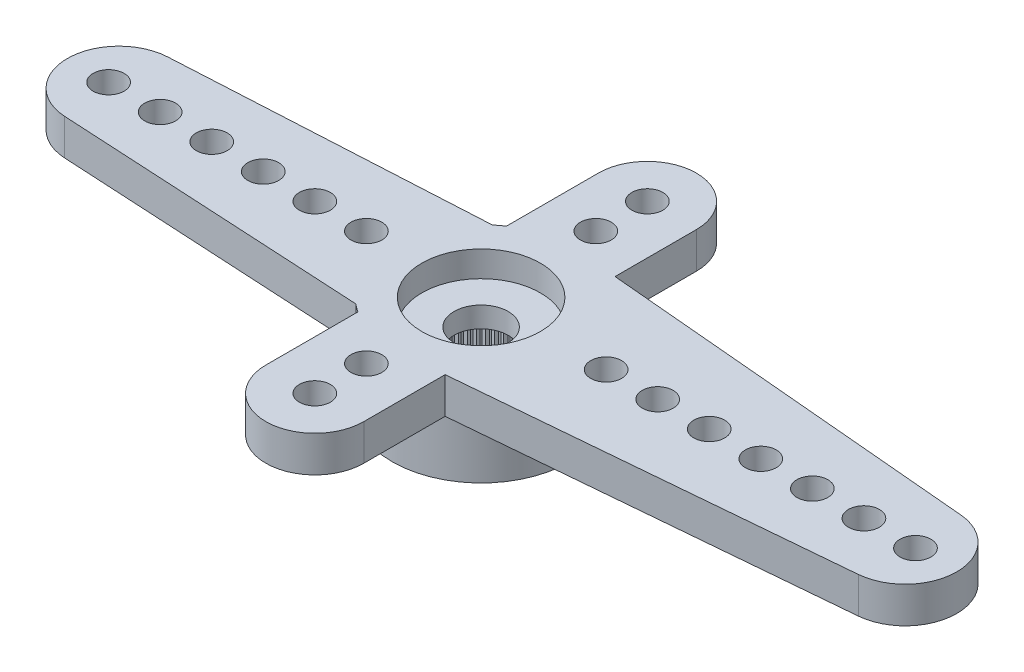
SolidWorks part; units mm, degrees
material "PVC Rígido"
ref_plane "Plano frontal" through (0, 0, 0) normal (0, 0, 1) x (1, 0, 0)
ref_plane "Plano superior" through (0, 0, 0) normal (0, 1, 0) x (1, 0, 0)
ref_plane "Plano direito" through (0, 0, 0) normal (1, 0, 0) x (0, 0, -1)
sketch "Esboço1" plane through (0, 0, 0) normal (0, 1, 0) x (1, 0, 0)
  line L0 (0, 0) -> (-14.05, 0) construction
  line L1 (-14.1591, 1.997) -> (-2.2091, 2.65)
  line L2 (-2.2091, -2.65) -> (-14.1591, -1.997)
  arc A0 (-2.2091, -2.65) -> (-2.2091, 2.65) centre (0, 0) ccw
  arc A1 (-14.1591, 1.997) -> (-14.1591, -1.997) centre (-14.05, 0) ccw
  dimension "D1" = 6.9
  dimension "D2" = 4
  dimension "D3" = 19.5
  dimension "D4" = 5.3
extrude "Ressalto-extrusão1" add sketch "Esboço1" against normal blind 1.4
sketch "Esboço2" plane through (0, -1.4, 0) normal (0, -1, 0) x (1, 0, 0)
  arc A0 (-2.2091, -2.65) -> (-2.2091, 2.65) centre (0, 0) ccw construction
  circle A1 centre (0, 0) radius 3.45
extrude "Ressalto-extrusão2" add sketch "Esboço2" along normal offset from surface (2.4 mm away) 3.8 up to face at (-7.242, 0, 0)
hole_wizard "Furo1" positions "Esboço9" profile "Esboço10" legacy end condition through all
sketch "Esboço9" plane through (0, 0, 0) normal (0, 1, 0) x (1, 0, 0)
  line L1 (-14.45, 0) -> (0, 0) construction
  arc A2 (-14.1591, 1.997) -> (-14.1591, -1.997) centre (-14.05, 0) ccw construction
  point P0 (-14.45, 0)
  point P19 (-16.05, 0)
  dimension "D1" = 1.6
sketch "Esboço10" plane through (-14.45, 0, 0) normal (1, 0, 0) x (0, 0, 1)
  line L0 (0, 0) -> (0, 3.8)
  line L1 (0, 3.8) -> (0.6, 3.8)
  line L2 (0.6, 3.8) -> (0.6, 0)
  line L3 (0.6, 0) -> (0, 0)
  line L4 (0, 110) -> (0, -10) construction
  dimension "Diameter" = 1.2
  dimension "Depth" = 3.8
pattern_linear "Padrão linear1" count 6 spacing 2 along (1, 0, 0) of "Furo1"
sketch "Esboço12" plane through (0, 0, 0) normal (0, 1, 0) x (1, 0, 0)
  line L0 (0.3041, 3.4366) -> (16.6263, 1.9922)
  line L1 (16.6263, -1.9922) -> (0.3041, -3.4366)
  arc A0 (-2.2091, -2.65) -> (-2.2091, 2.65) centre (0, 0) ccw construction
  arc A1 (0.3041, -3.4366) -> (0.3041, 3.4366) centre (0, 0) ccw
  arc A2 (16.6263, 1.9922) -> (16.6263, -1.9922) centre (16.45, 0) cw
  arc A3 (-14.1591, 1.997) -> (-14.1591, -1.997) centre (-14.05, 0) ccw construction
  point P11 (0, 0)
  dimension "D1" = 2
  dimension "D2" = 34.5
extrude "Ressalto-extrusão3" add sketch "Esboço12" against normal up to surface (1.4 mm away) up to face at (-12.45, -1.4, 0.6)
hole_wizard "Furo2" positions "Esboço13" profile "Esboço14" legacy end condition through all
sketch "Esboço13" plane through (0, 0, 0) normal (0, 1, 0) x (1, 0, 0)
  line L0 (0, 0) -> (16.85, 0) construction
  arc A0 (16.6263, -1.9922) -> (16.6263, 1.9922) centre (16.45, 0) ccw construction
  point P0 (16.85, 0)
  point P6 (18.45, 0)
  dimension "D1" = 1.6
sketch "Esboço14" plane through (16.85, 0, 0) normal (1, 0, 0) x (0, 0, 1)
  line L0 (0, 0) -> (0, 3.8)
  line L1 (0, 3.8) -> (0.6, 3.8)
  line L2 (0.6, 3.8) -> (0.6, 0)
  line L3 (0.6, 0) -> (0, 0)
  line L4 (0, 110) -> (0, -10) construction
  dimension "Diameter" = 1.2
  dimension "Depth" = 3.8
pattern_linear "Padrão linear2" count 7 spacing 2 along (-1, 0, 0) of "Furo2"
sketch "Esboço16" plane through (0, 0, 0) normal (0, 1, 0) x (1, 0, 0)
  line L0 (0, -6.45) -> (0, 6.45) construction
  line L1 (-1.9, -6.45) -> (-1.9, 6.45)
  line L2 (1.9, -6.45) -> (1.9, 6.45)
  arc A0 (-1.9, -6.45) -> (1.9, -6.45) centre (0, -6.45) ccw
  arc A1 (1.9, 6.45) -> (-1.9, 6.45) centre (0, 6.45) ccw
  point P2 (0, 0)
  dimension "D2" = 16.7
  dimension "D1" = 3.8
extrude "Ressalto-extrusão4" add sketch "Esboço16" against normal up to surface (1.4 mm away) up to face at (14.85, -1.4, 0.6)
hole_wizard "Furo3" positions "Esboço17" profile "Esboço18" legacy end condition through all
sketch "Esboço17" plane through (0, 0, 0) normal (0, 1, 0) x (1, 0, 0)
  point P0 (0, -6.45)
sketch "Esboço18" plane through (0, 0, 6.45) normal (1, 0, 0) x (0, 0, 1)
  line L0 (0, 0) -> (0, 3.8)
  line L1 (0, 3.8) -> (0.6, 3.8)
  line L2 (0.6, 3.8) -> (0.6, 0)
  line L3 (0.6, 0) -> (0, 0)
  line L4 (0, 110) -> (0, -10) construction
  dimension "Diameter" = 1.2
  dimension "Depth" = 3.8
pattern_linear "Padrão linear3" count 2 spacing 2 along (0, 0, -1) of "Furo3"
pattern_circular "PadrãoCircular1" count 2 over 360 about axis through (0, 0, 0) along (0, 1, 0) of "Padrão linear3", "Furo3"
hole_wizard "Furo4" positions "Esboço3" profile "Esboço4" legacy
sketch "Esboço3" plane through (0, -3.8, 0) normal (0, -1, 0) x (-1, 0, 0)
  point P0 (0, 0)
sketch "Esboço4" plane through (0, -3.8, 0) normal (1, 0, 0) x (0, 0, -1)
  line L0 (0, 0) -> (0, 2)
  line L1 (0, 2) -> (2.475, 2)
  line L2 (2.475, 2) -> (2.475, 0)
  line L3 (2.475, 0) -> (0, 0)
  line L4 (0, 110) -> (0, -10) construction
  dimension "Diameter" = 4.95
  dimension "Depth" = 2
hole_wizard "Furo5" positions "Esboço5" profile "Esboço6" legacy
sketch "Esboço5" plane through (0, 0, 0) normal (0, 1, 0) x (1, 0, 0)
  point P0 (0, 0)
sketch "Esboço6" plane through (0, 0, 0) normal (1, 0, 0) x (0, 0, 1)
  line L0 (0, 0) -> (0, 1)
  line L1 (0, 1) -> (2.3, 1)
  line L2 (2.3, 1) -> (2.3, 0)
  line L3 (2.3, 0) -> (0, 0)
  line L4 (0, 110) -> (0, -10) construction
  dimension "Diameter" = 4.6
  dimension "Depth" = 1
hole_wizard "Furo6" positions "Esboço7" profile "Esboço8" legacy end condition through all
sketch "Esboço7" plane through (0, 0, 0) normal (0, 1, 0) x (1, 0, 0)
  point P0 (0, 0)
sketch "Esboço8" plane through (0, 0, 0) normal (1, 0, 0) x (0, 0, 1)
  line L0 (0, 0) -> (0, 3.8)
  line L1 (0, 3.8) -> (1.05, 3.8)
  line L2 (1.05, 3.8) -> (1.05, 0)
  line L3 (1.05, 0) -> (0, 0)
  line L4 (0, 110) -> (0, -10) construction
  dimension "Diameter" = 2.1
  dimension "Depth" = 3.8
sketch "Esboço11" plane through (0, -3.8, 0) normal (0, -1, 0) x (1, 0, 0)
  line L0 (-0.0981, 2.4731) -> (0, 2.375)
  line L1 (0, 2.375) -> (0.0981, 2.4731)
  line L2 (0, 0) -> (0, 2.475) construction
  circle A0 centre (0, 0) radius 2.375 construction
  circle A1 centre (0, 0) radius 2.475
  arc A2 (0.0981, 2.4731) -> (-0.0981, 2.4731) centre (0, 0) ccw
  dimension "D3" = 4.75
  dimension "D2" = 0.1
  dimension "D1" = 0
extrude "Ressalto-extrusão5" add sketch "Esboço11" against normal up to surface (2 mm away) up to face at (0, -1.8, 1.05)
pattern_circular "PadrãoCircular2" count 60 over 360 about axis through (0, 0, 0) along (0, 1, 0) of "Ressalto-extrusão5"
